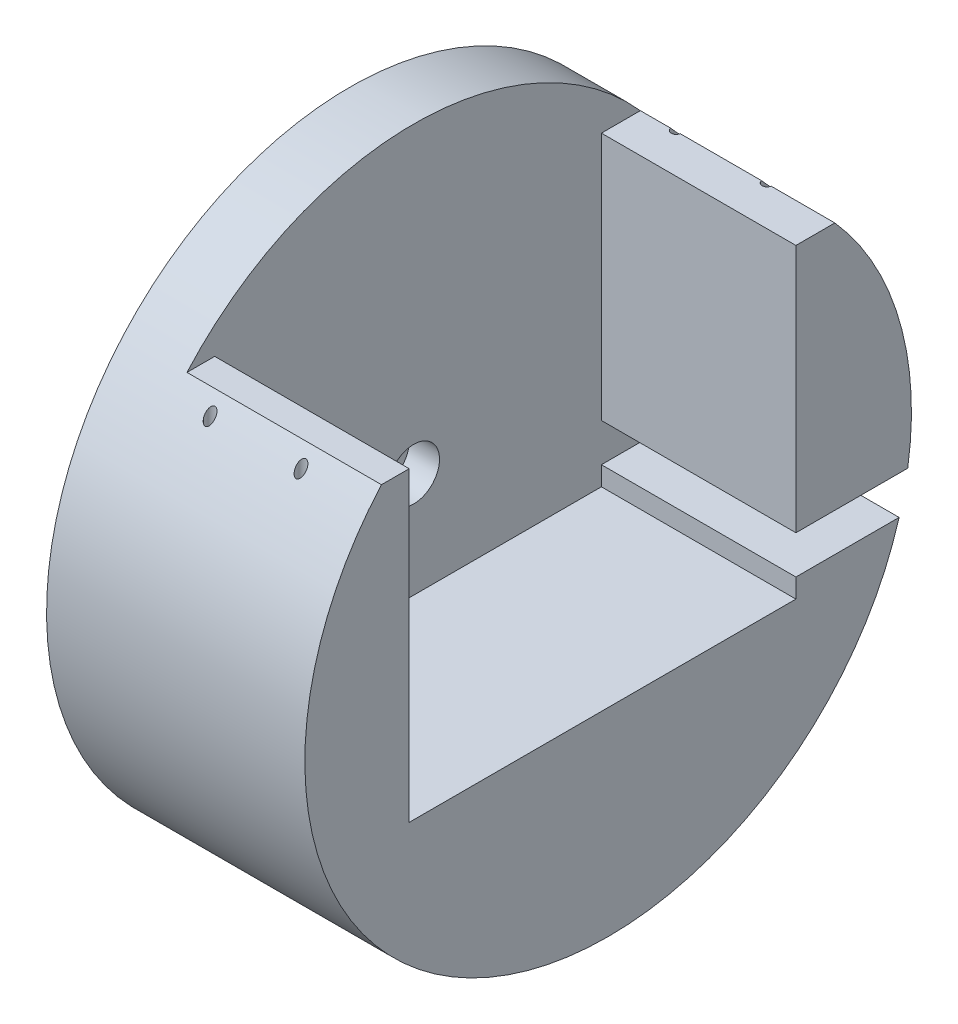
SolidWorks part; units mm, degrees
material "ABS PC"
ref_plane "Front Plane" through (0, 0, 0) normal (0, 0, 1) x (1, 0, 0)
ref_plane "Top Plane" through (0, 0, 0) normal (0, 1, 0) x (1, 0, 0)
ref_plane "Right Plane" through (0, 0, 0) normal (1, 0, 0) x (0, 0, -1)
sketch "Sketch1" plane through (0, 0, 0) normal (1, 0, 0) x (0, 0, -1)
  circle A0 centre (0, 0) radius 31.6865
  dimension "D1" = 63.373
extrude "Boss-Extrude1" add sketch "Sketch1" along normal blind 26.9875
sketch "Sketch3" plane through (26.9875, 0, 0) normal (1, 0, 0) x (0, 0, -1)
  line L0 (-28.4027, 14.0471) -> (-27.7851, 21.05)
  line L1 (-27.7851, 21.05) -> (-20.7851, 21.05)
  line L2 (-20.7851, 21.05) -> (-20.7851, -10.95)
  line L3 (-20.7851, -10.95) -> (19.6149, -10.95)
  line L4 (19.6149, -10.95) -> (19.6149, -8.95)
  line L5 (19.6149, -8.95) -> (30.3962, -8.95)
  line L6 (19.6149, 21.05) -> (19.6149, -4.95)
  line L7 (19.6149, -4.95) -> (31.2975, -4.95)
  line L8 (19.6149, 21.05) -> (23.684, 21.05)
  circle A0 centre (0, 0) radius 31.6865 construction
  circle A1 centre (0, 0) radius 33.5064
  circle M2 centre (0, 0) radius 31.6865
  dimension "D2" = 4
  dimension "D4" = 32
  dimension "D5" = 2
extrude "Cut-Extrude1" cut sketch "Sketch3" against normal blind 20.32 contours L6 L8 L1 L2 L3 L4 L5 L7 M2 | A1
sketch "Sketch5" plane through (0, 21.05, 0) normal (0, 1, 0) x (1, 0, 0)
  circle A0 centre (10.33, -24.9326) radius 0.508
  circle A1 centre (19.83, -24.9326) radius 0.508
  circle A2 centre (10.33, 23.7623) radius 0.508
  circle A3 centre (19.83, 23.7623) radius 0.508
  dimension "D1" = 1.016
  dimension "D2" = 1.016
  dimension "D3" = 1.016
  dimension "D4" = 1.016
extrude "Cut-Extrude2" cut sketch "Sketch5" against normal blind 12.7
sketch "Sketch6" plane through (0, 0, 0) normal (-1, 0, 0) x (0, 0, 1)
  circle A0 centre (-1.5399, 19.9406) radius 0.508
  dimension "D1" = 1.016
extrude "Cut-Extrude3" cut sketch "Sketch6" against normal blind 3.556
sketch "Sketch7" plane through (6.6675, 0, 0) normal (1, 0, 0) x (0, 0, -1)
  circle A0 centre (0, 0) radius 2.6987
  dimension "D1" = 5.3975
extrude "Boss-Extrude2" add sketch "Sketch7" against normal blind 3.175
sketch "Sketch11" plane through (6.6675, 0, 0) normal (1, 0, 0) x (0, 0, -1)
  circle A0 centre (0, 0) radius 2.6987
  dimension "D1" = 5.3975
extrude "Cut-Extrude6" cut sketch "Sketch11" against normal blind 3.175
sketch "Sketch12" plane through (0, 0, 0) normal (-1, 0, 0) x (0, 0, 1)
  circle A0 centre (0, 0) radius 1.651
  dimension "D1" = 3.302
extrude "Cut-Extrude7" cut sketch "Sketch12" against normal blind 9.017
